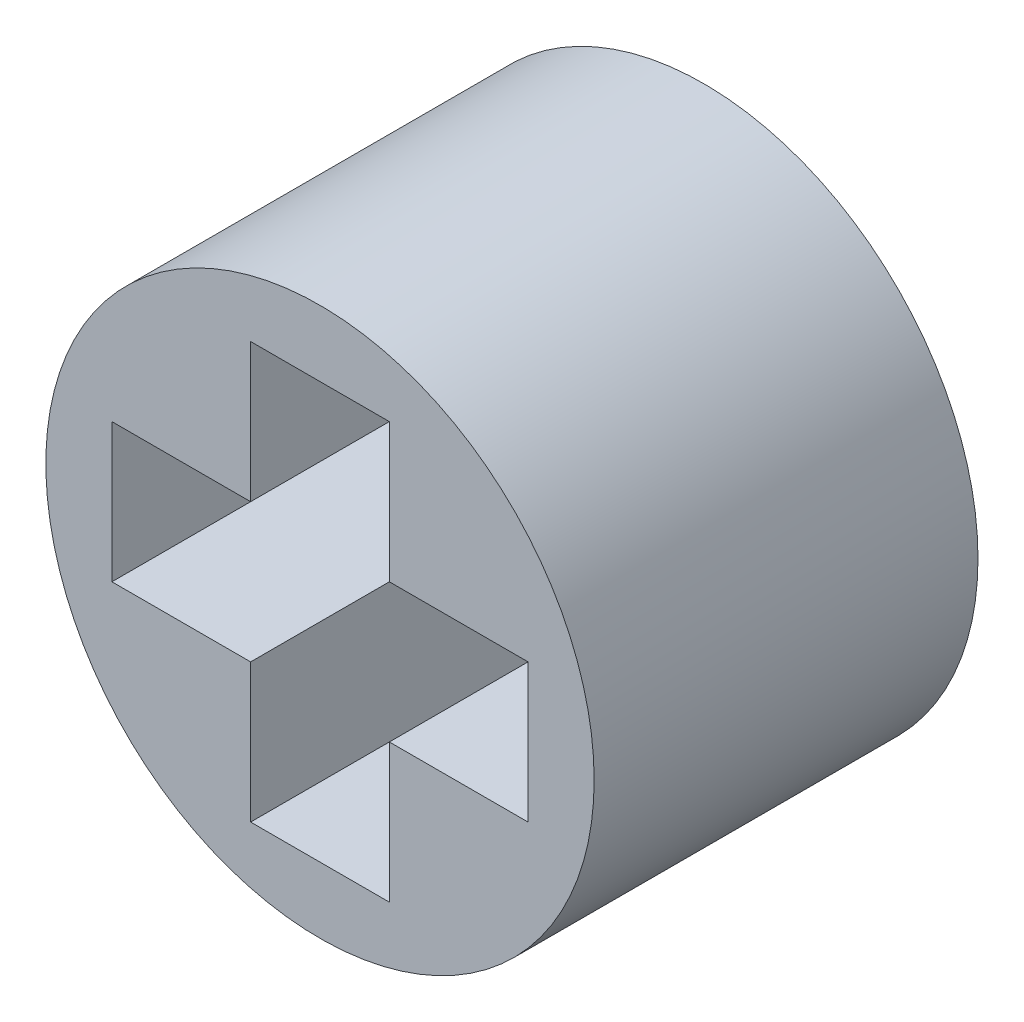
SolidWorks part; units mm, degrees
ref_plane "Front Plane" through (0, 0, 0) normal (0, 0, 1) x (1, 0, 0)
ref_plane "Top Plane" through (0, 0, 0) normal (0, 1, 0) x (1, 0, 0)
ref_plane "Right Plane" through (0, 0, 0) normal (1, 0, 0) x (0, 0, -1)
sketch "Sketch1" plane through (0, 0, 0) normal (0, 0, 1) x (1, 0, 0)
  line L0 (-4, 0) -> (4, 0) construction
  line L1 (0, 4) -> (0, -4) construction
  line L2 (-3.7947, 1.2649) -> (-3.7947, -1.2649)
  line L3 (-3.7947, 1.2649) -> (-1.2649, 1.2649)
  line L4 (-1.2649, 1.2649) -> (-1.2649, 3.7947)
  line L5 (-1.2649, 3.7947) -> (1.2649, 3.7947)
  line L6 (1.2649, 3.7947) -> (1.2649, 1.2649)
  line L7 (1.2649, 1.2649) -> (3.7947, 1.2649)
  line L8 (3.7947, 1.2649) -> (3.7947, -1.2649)
  line L9 (3.7947, -1.2649) -> (1.2649, -1.2649)
  line L10 (1.2649, -1.2649) -> (1.2649, -3.7947)
  line L11 (1.2649, -3.7947) -> (-1.2649, -3.7947)
  line L12 (-1.2649, -3.7947) -> (-1.2649, -1.2649)
  line L13 (-1.2649, -1.2649) -> (-3.7947, -1.2649)
  circle A0 centre (0, 0) radius 4 construction
  circle A1 centre (0, 0) radius 5
  point P6 (0, 0)
  point P8 (0, 0)
  point P12 (-3.7947, 0)
  point P23 (0, 3.7947)
  dimension "D1" = 8
  dimension "D2" = 10
extrude "Boss-Extrude1" add sketch "Sketch1" along normal blind 7
